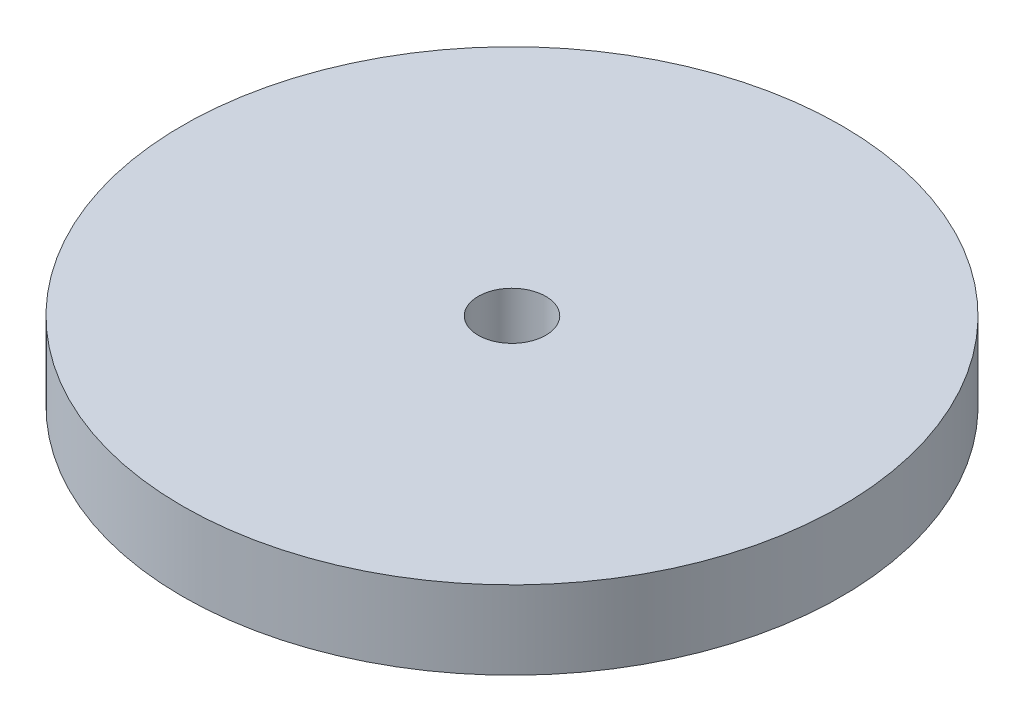
SolidWorks part; units mm, degrees
ref_plane "Front Plane" through (0, 0, 0) normal (0, 0, 1) x (1, 0, 0)
ref_plane "Top Plane" through (0, 0, 0) normal (0, 1, 0) x (1, 0, 0)
ref_plane "Right Plane" through (0, 0, 0) normal (1, 0, 0) x (0, 0, -1)
sketch "Sketch1" plane through (0, 0, 0) normal (0, 1, 0) x (1, 0, 0)
  circle A0 centre (0, 0) radius 40
  circle A1 centre (0, 0) radius 4.1
  dimension "D1" = 80
  dimension "D2" = 8.2
extrude "Boss-Extrude1" add sketch "Sketch1" along normal blind 9.5
